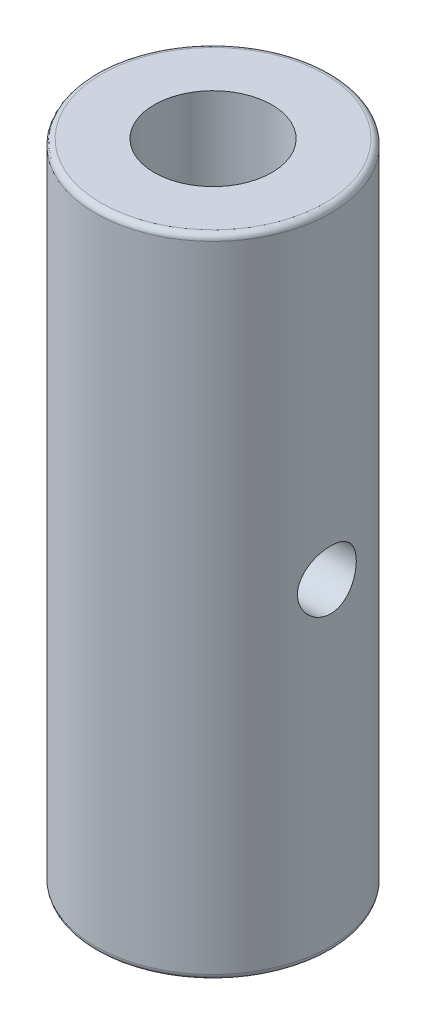
SolidWorks part; units mm, degrees
ref_plane "前视基准面" through (0, 0, 0) normal (0, 0, 1) x (1, 0, 0)
ref_plane "上视基准面" through (0, 0, 0) normal (0, 1, 0) x (1, 0, 0)
ref_plane "右视基准面" through (0, 0, 0) normal (1, 0, 0) x (0, 0, -1)
other "Configuration Table"
sketch "草图1" plane through (0, 0, 0) normal (0, 1, 0) x (1, 0, 0)
  circle A0 centre (0, 0) radius 20
  circle A1 centre (0, 0) radius 10
extrude "凸台-拉伸1" add sketch "草图1" along normal blind 110
sketch "草图2" plane through (0, 0, 0) normal (1, 0, 0) x (0, 0, -1)
  line L0 (0, 110) -> (0, 0) construction
  line L1 (20, 110) -> (-20, 110) construction
  line L2 (-20, 0) -> (20, 0) construction
  circle A0 centre (0, 55) radius 5
extrude "切除-拉伸1" cut sketch "草图2" against normal through all and the other way through all
fillet "圆角1" radius 1 2 edges at (0, 0, 20) (0, 110, 20)
